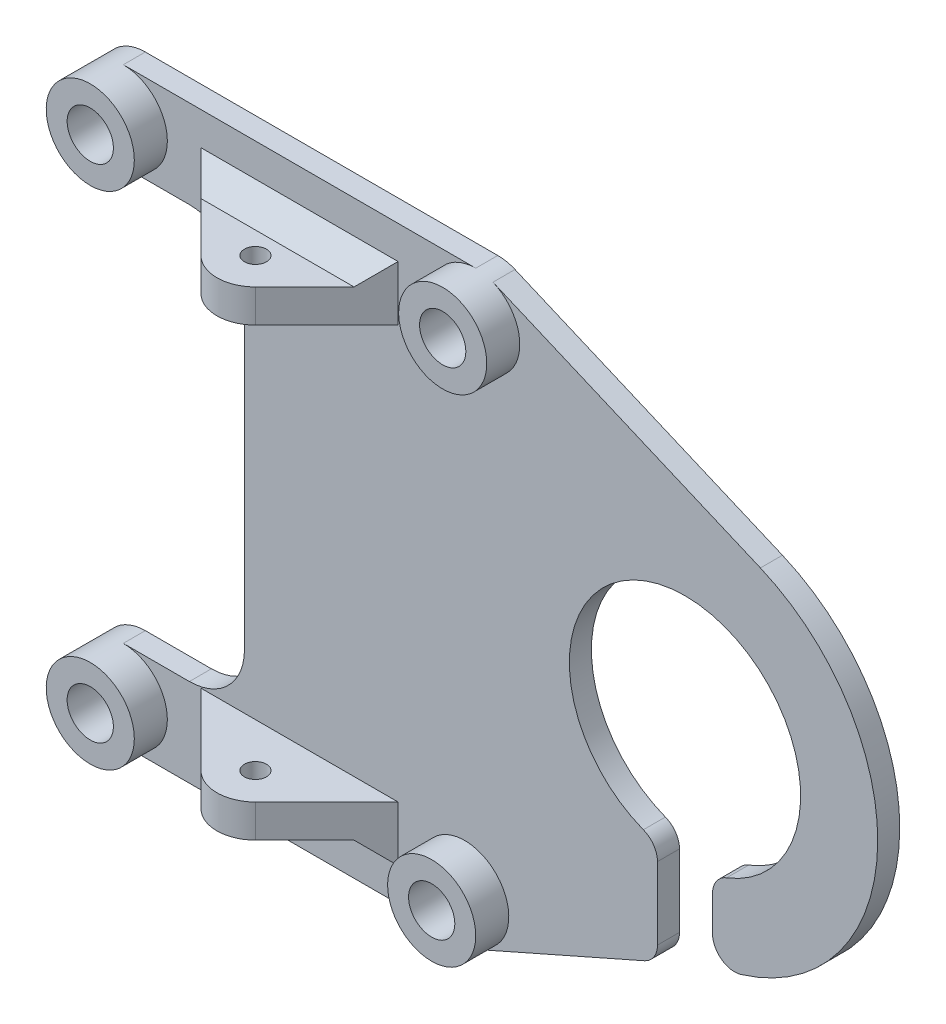
SolidWorks part; units mm, degrees
ref_plane "Front Plane" through (0, 0, 0) normal (0, 0, 1) x (1, 0, 0)
ref_plane "Top Plane" through (0, 0, 0) normal (0, 1, 0) x (1, 0, 0)
ref_plane "Right Plane" through (0, 0, 0) normal (1, 0, 0) x (0, 0, -1)
sketch "Sketch1" plane through (0, 0, 0) normal (0, 0, 1) x (1, 0, 0)
  line L0 (-16, -26.75) -> (16, -26.75)
  line L1 (-5, -13.75) -> (-5, 13.75)
  line L3 (-16, 26.75) -> (16, 26.75)
  line L4 (17.5654, 26.431) -> (41.8485, 16.1043)
  line L6 (37.5, -11.6619) -> (37.5, -14.8324)
  line L7 (37.5, -13.75) -> (32.5, -13.75) construction
  line L8 (-16, 18.75) -> (-10, 18.75)
  line L9 (0, 0) -> (0, 5.8305) construction
  line L10 (0, 0) -> (2.3927, 0) construction
  line L11 (32.5, -11.6619) -> (32.5, -18.2256)
  line L12 (31.308, -20.0551) -> (16.6657, -26.5217)
  line L14 (-16, -18.75) -> (-10, -18.75)
  arc A0 (-16, 26.75) -> (-16, 18.75) centre (-16, 22.75) ccw
  arc A3 (-16, -18.75) -> (-16, -26.75) centre (-16, -22.75) ccw
  circle A4 centre (-16, 22.75) radius 2.1
  circle A5 centre (16, 22.75) radius 2.1
  circle A6 centre (15, -22.75) radius 2.1
  circle A7 centre (-16, -22.75) radius 2.1
  arc A8 (-10, 18.75) -> (-5, 13.75) centre (-10, 13.75) cw
  arc A9 (16, 26.75) -> (17.5654, 26.431) centre (16, 22.75) cw
  arc A10 (41.8485, 16.1043) -> (40.0806, -16.7463) centre (35, 0) cw
  arc A11 (-10, -18.75) -> (-5, -13.75) centre (-10, -13.75) ccw
  arc A12 (16, -26.75) -> (16.6657, -26.5217) centre (15, -22.75) ccw
  arc A13 (38.78, -9.796) -> (31.22, -9.796) centre (35, 0) ccw
  arc A14 (40.0806, -16.7463) -> (37.5, -14.8324) centre (39.5, -14.8324) cw
  arc A15 (32.5, -18.2256) -> (31.308, -20.0551) centre (30.5, -18.2256) cw
  arc A16 (38.78, -9.796) -> (37.5, -11.6619) centre (39.5, -11.6619) ccw
  arc A17 (31.22, -9.796) -> (32.5, -11.6619) centre (30.5, -11.6619) cw
  point P1 (0, 0)
  point P20 (-5, 0)
  point P26 (-5, 18.75)
  point P36 (35, -13.75)
  point P37 (5, 18.75)
  point P38 (42.721, -14.3299)
  point P40 (5, -18.75)
  point P43 (-5, -18.75)
  point P44 (47.7388, -12.194)
  point P45 (0, 0)
  point P48 (37.5, -17.3205)
  point P52 (0, 26.75)
  point P56 (0, 0)
  point P57 (0, 0)
  point P58 (17.4857, -23.1339)
  dimension "D1" = 4.2
  dimension "D2" = 8
  dimension "D4" = 5
  dimension "D8" = 2
  dimension "D9" = 10.5
  dimension "D10" = 7
  dimension "D3" = 32
  dimension "D5" = 37.5
  dimension "D6" = 35
  dimension "D7" = 5
  dimension "D11" = 5
extrude "Boss-Extrude1" add sketch "Sketch1" along normal blind 2
sketch "Sketch2" plane through (0, -26.75, 0) normal (0, -1, 0) x (1, 0, 0)
  line L0 (-16, 2) -> (16, 2) construction
  line L1 (-2.4749, 8.4749) -> (-8.9497, 2)
  line L2 (-8.9497, 2) -> (8.9497, 2)
  line L3 (8.9497, 2) -> (2.4749, 8.4749)
  circle A0 centre (0, 6) radius 1
  arc A1 (2.4749, 8.4749) -> (-2.4749, 8.4749) centre (0, 6) ccw
  point P2 (1.6753, 8.4749)
  point P6 (0, 0)
  point P10 (0, 0)
  dimension "D1" = 2
  dimension "D2" = 2.5
  dimension "D3" = 4
extrude "Boss-Extrude2" add sketch "Sketch2" along normal blind 3 from surface at -8 starting at face at (-13, -18.75, 1)
chamfer "Chamfer1" distance 2 angle 45 1 edges at (0, -21.75, 2)
mirror "Mirror2" about plane through (0, 0, 0) normal (0, 1, 0) of "Chamfer1", "Boss-Extrude2"
sketch "Sketch3" plane through (0, 0, 2) normal (0, 0, 1) x (1, 0, 0)
  circle A0 centre (-16, -22.75) radius 4
  circle A1 centre (-16, -22.75) radius 2.1
  circle A2 centre (15, -22.75) radius 4
  circle A3 centre (15, -22.75) radius 2.1
  circle A4 centre (16, 22.75) radius 4
  circle A5 centre (16, 22.75) radius 2.1
  circle A6 centre (-16, 22.75) radius 4
  circle A7 centre (-16, 22.75) radius 2.1
  circle A8 centre (-16, -22.75) radius 2.1 construction
  arc A9 (-16, -18.75) -> (-16, -26.75) centre (-16, -22.75) ccw construction
extrude "Boss-Extrude3" add sketch "Sketch3" along normal blind 3
